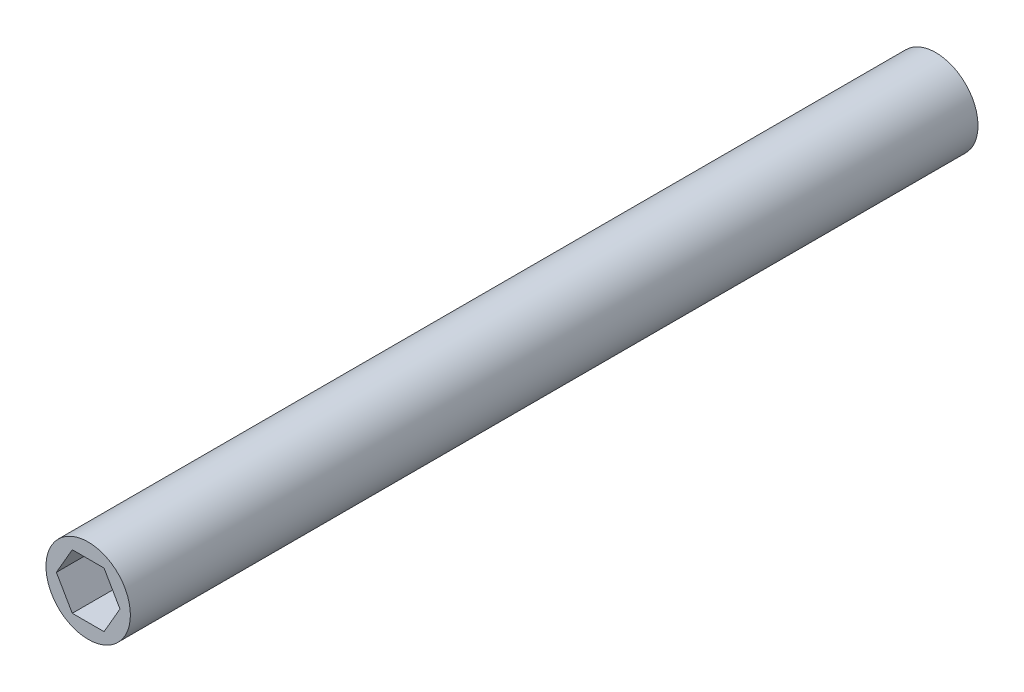
SolidWorks part; units mm, degrees
ref_plane "Front Plane" through (0, 0, 0) normal (0, 0, 1) x (1, 0, 0)
ref_plane "Top Plane" through (0, 0, 0) normal (0, 1, 0) x (1, 0, 0)
ref_plane "Right Plane" through (0, 0, 0) normal (1, 0, 0) x (0, 0, -1)
sketch "Sketch8" plane through (0, 0, 0) normal (0, 0, 1) x (1, 0, 0)
  circle A0 centre (0, 0) radius 6.3246
  dimension "D1" = 12.6492
extrude "Boss-Extrude7" add sketch "Sketch8" along normal blind 127 contours A0
sketch "Sketch9" plane through (0, 0, 0) normal (0, 0, 1) x (1, 0, 0)
  line L1 (-1.5875, -5.5245) -> (1.5875, -5.5245)
  line L2 (-1.5875, -5.5245) -> (-1.5875, -7.1247)
  line L3 (-1.5875, -7.1247) -> (1.5875, -7.1247)
  line L4 (1.5875, -5.5245) -> (1.5875, -7.1247)
  line L5 (-1.5875, -5.5245) -> (1.5875, -7.1247) construction
  line L6 (-1.5875, -7.1247) -> (1.5875, -5.5245) construction
  circle A0 centre (0, 0) radius 6.3246 construction
  point P0 (0, -6.3246)
  dimension "D1" = 1.6002
  dimension "D2" = 3.175
extrude "Boss-Extrude8" add sketch "Sketch9" along normal blind 49.911
sketch "Sketch10" plane through (-1.5875, 0, 0) normal (-1, 0, 0) x (0, 0, 1)
  line L0 (49.911, -7.1247) -> (0, -7.1247) construction
  line L1 (0, -6.1221) -> (21.336, -6.1221)
  line L2 (0, -6.1221) -> (0, -7.1247)
  line L3 (0, -7.1247) -> (21.336, -7.1247)
  line L4 (21.336, -6.1221) -> (21.336, -7.1247)
  dimension "D1" = 21.336
extrude "Cut-Extrude1" cut sketch "Sketch10" against normal blind 3.937
sketch "Sketch11" plane through (0, 0, 127) normal (0, 0, 1) x (1, 0, 0)
  line L1 (4.7625, 0) -> (2.3812, 4.1244)
  line L2 (2.3812, 4.1244) -> (-2.3813, 4.1244)
  line L3 (-2.3813, 4.1244) -> (-4.7625, 0)
  line L4 (-4.7625, 0) -> (-2.3813, -4.1244)
  line L5 (-2.3813, -4.1244) -> (2.3813, -4.1244)
  line L6 (2.3813, -4.1244) -> (4.7625, 0)
  circle A0 centre (0, 0) radius 4.1244 construction
  dimension "D1" = 4.7625
extrude "Cut-Extrude2" cut sketch "Sketch11" against normal blind 8.89
